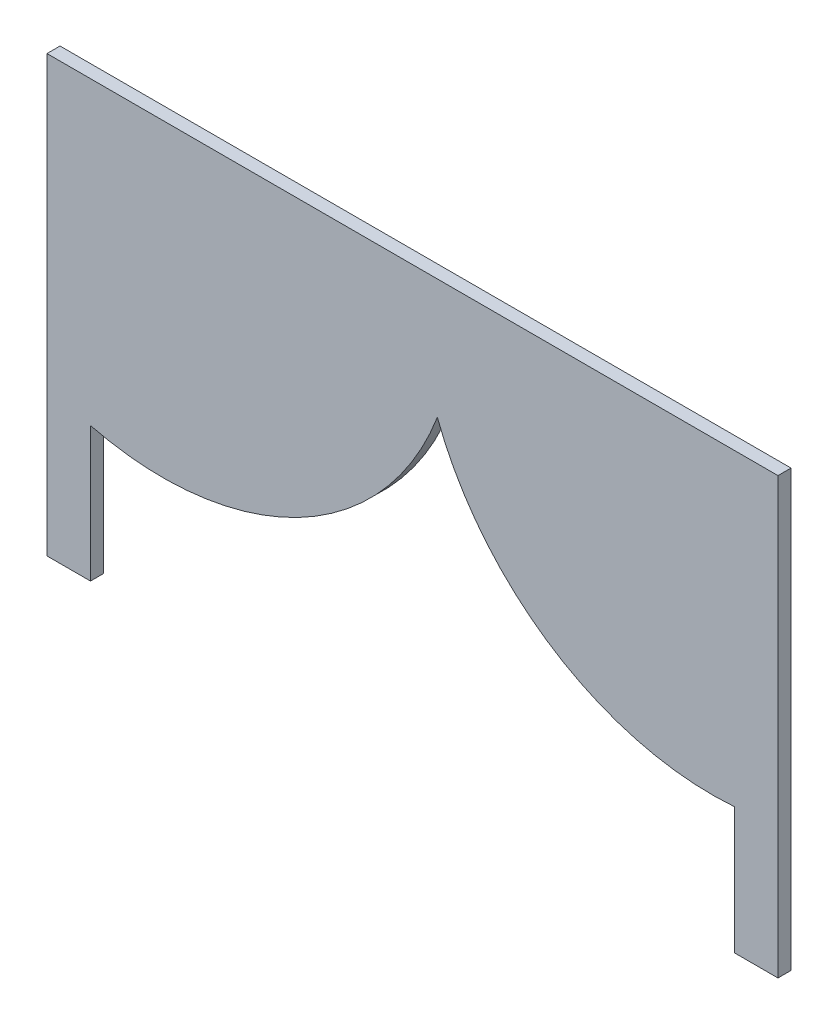
SolidWorks part; units mm, degrees
ref_plane "Alzado" through (0, 0, 0) normal (0, 0, 1) x (1, 0, 0)
ref_plane "Planta" through (0, 0, 0) normal (0, 1, 0) x (1, 0, 0)
ref_plane "Vista lateral" through (0, 0, 0) normal (1, 0, 0) x (0, 0, -1)
sketch "Croquis1" plane through (0, 0, 0) normal (0, 0, 1) x (1, 0, 0)
  line L0 (68.2872, -24.3078) -> (68.2872, -43.4005)
  line L1 (78.2872, 46.5995) -> (-89.7128, 46.5995)
  line L2 (78.2872, 46.5995) -> (78.2872, -53.4005)
  line L3 (78.2872, -53.4005) -> (68.2872, -53.4005)
  line L4 (-89.7128, 46.5995) -> (-89.7128, -53.4005)
  line L6 (78.2872, -53.4005) -> (68.2872, -46.5794) construction
  line L8 (-79.7128, -22.4459) -> (-79.7128, -43.4005)
  line L10 (68.2872, -43.4005) -> (68.2872, -53.4005)
  line L11 (-79.7128, -43.4005) -> (-79.7128, -53.4005)
  line L12 (0, 0) -> (0, 19.0451) construction
  line L13 (68.2872, -43.4005) -> (-79.7128, -43.4005) construction
  line L14 (-79.7128, -53.4005) -> (-89.7128, -53.4005)
  line L15 (78.2872, -53.4005) -> (-89.7128, -53.4005) construction
  line L16 (0, 67.1316) -> (0, 95.5933) construction
  line L17 (-79.7128, 36.5995) -> (-79.7128, -43.4005) construction
  line L18 (68.2872, 36.5995) -> (-79.7128, 36.5995) construction
  line L19 (68.2872, 36.5995) -> (68.2872, -43.4005) construction
  arc A0 (-79.7128, -22.4459) -> (0, 19.0451) centre (-63.1692, 43.0883) ccw
  arc A2 (68.2872, -24.3078) -> (0, 19.0451) centre (63.1692, 43.0883) cw
  point P0 (0, 0)
  point P18 (0, 0)
  point P20 (0, 0)
  dimension "D1" = 168
  dimension "D2" = 100
  dimension "D3" = 10
extrude "Saliente-Extruir1" add sketch "Croquis1" along normal blind 3
